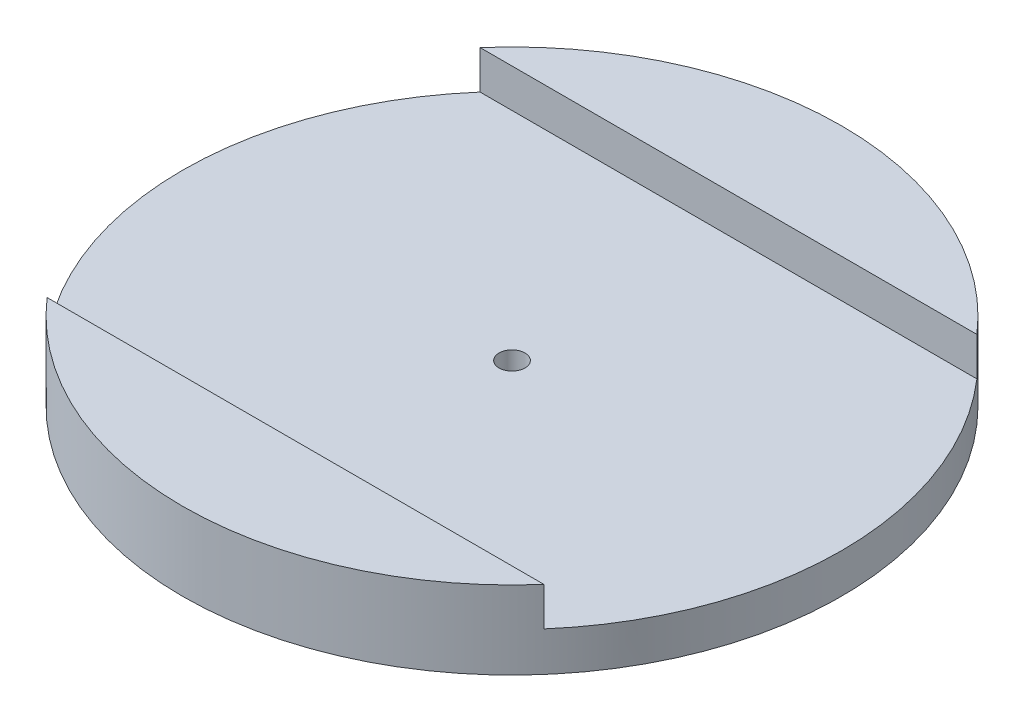
SolidWorks part; units mm, degrees
ref_plane "Front Plane" through (0, 0, 0) normal (0, 0, 1) x (1, 0, 0)
ref_plane "Top Plane" through (0, 0, 0) normal (0, 1, 0) x (1, 0, 0)
ref_plane "Right Plane" through (0, 0, 0) normal (1, 0, 0) x (0, 0, -1)
sketch "Sketch1" plane through (0, 0, 0) normal (0, 1, 0) x (1, 0, 0)
  circle A0 centre (0, 0) radius 76
  dimension "D1" = 152
extrude "Boss-Extrude1" add sketch "Sketch1" along normal blind 18 contours A0
sketch "Sketch2" plane through (0, 18, 0) normal (0, 1, 0) x (1, 0, 0)
  line L0 (-76, 0) -> (76, 0) construction
  line L1 (-58.008, 0) -> (58.008, 0) construction
  line L2 (-58.008, 49.9318) -> (58.008, 49.9318)
  line L3 (-58.008, -49.9318) -> (58.008, -49.9318)
  circle A0 centre (0, 0) radius 76 construction
  arc A1 (-58.008, 49.9318) -> (-58.008, -49.9318) centre (-58.008, 0) ccw
  arc A2 (58.008, -49.9318) -> (58.008, 49.9318) centre (58.008, 0) ccw
  point P7 (0, 0)
extrude "Cut-Extrude4" cut sketch "Sketch2" against normal blind 8.89
sketch "Sketch5" plane through (0, 9.11, 0) normal (0, 1, 0) x (1, 0, 0)
  line L0 (0, 3) -> (0, -3)
  circle A0 centre (0, 0) radius 3
extrude "Cut-Extrude5" cut sketch "Sketch5" against normal blind 20 contours A0
